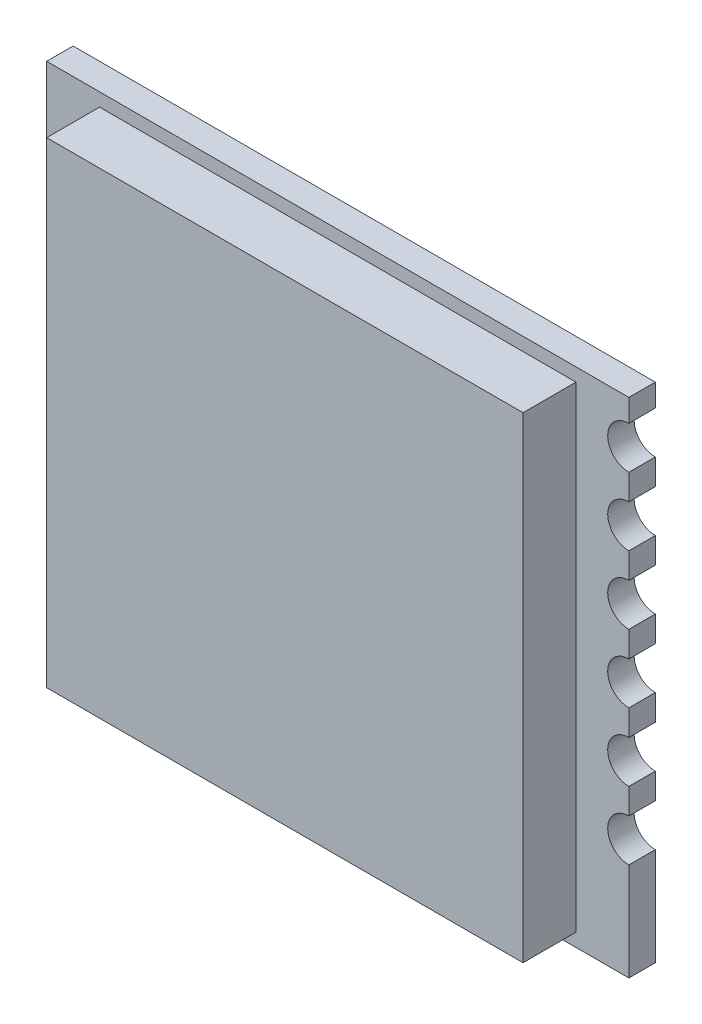
SolidWorks part; units mm, degrees
other "Детальный элемент1"
ref_plane "Спереди" through (0, 0, 0) normal (0, 0, 1) x (1, 0, 0)
ref_plane "Сверху" through (0, 0, 0) normal (0, 1, 0) x (1, 0, 0)
ref_plane "Справа" through (0, 0, 0) normal (1, 0, 0) x (0, 0, -1)
sketch "Эскиз1" plane through (0, 0, 0) normal (0, 0, 1) x (1, 0, 0)
  line L1 (11, -9.5) -> (-11, -9.5)
  line L2 (11, -9.5) -> (11, 9.5)
  line L3 (11, 9.5) -> (-11, 9.5)
  line L4 (-11, -9.5) -> (-11, 9.5)
  line L5 (11, -9.5) -> (-11, 9.5) construction
  line L6 (11, 9.5) -> (-11, -9.5) construction
  point P0 (0, 0)
extrude "Бобышка-Вытянуть1" add sketch "Эскиз1" along normal blind 1
sketch "Эскиз2" plane through (0, 0, 1) normal (0, 0, 1) x (1, 0, 0)
  line L1 (9, -9) -> (-9, -9)
  line L2 (9, -9) -> (9, 9)
  line L3 (9, 9) -> (-9, 9)
  line L4 (-9, -9) -> (-9, 9)
  line L5 (9, -9) -> (-9, 9) construction
  line L6 (9, 9) -> (-9, -9) construction
  point P0 (0, 0)
  dimension "D1" = 18
extrude "Бобышка-Вытянуть2" add sketch "Эскиз2" along normal blind 2
sketch "Эскиз3" plane through (0, 0, 3) normal (0, 0, 1) x (1, 0, 0)
  line L0 (0, 0) -> (0, 9) construction
  line L1 (9, 9) -> (-9, 9) construction
  line L2 (-11, 9.5) -> (-11, -9.5) construction
  line L3 (-11, -9.5) -> (11, -9.5) construction
  line L4 (-11, -4.2) -> (-11, -5.8)
  line L5 (-11, -1.63) -> (-11, -3.23)
  line L6 (-11, 0.94) -> (-11, -0.66)
  line L7 (-11, 3.51) -> (-11, 1.91)
  line L8 (-11, 6.08) -> (-11, 4.48)
  line L9 (11, -4.2) -> (11, -5.8)
  line L10 (11, -1.63) -> (11, -3.23)
  line L11 (11, 0.94) -> (11, -0.66)
  line L12 (11, 3.51) -> (11, 1.91)
  line L13 (11, 6.08) -> (11, 4.48)
  line L14 (11, 8.65) -> (11, 7.05)
  arc A0 (-11, -5.8) -> (-11, -4.2) centre (-11, -5) ccw
  arc A1 (-11, -3.23) -> (-11, -1.63) centre (-11, -2.43) ccw
  arc A2 (-11, -0.66) -> (-11, 0.94) centre (-11, 0.14) ccw
  arc A3 (-11, 1.91) -> (-11, 3.51) centre (-11, 2.71) ccw
  arc A4 (-11, 4.48) -> (-11, 6.08) centre (-11, 5.28) ccw
  arc A5 (11, -5.8) -> (11, -4.2) centre (11, -5) cw
  arc A6 (11, -3.23) -> (11, -1.63) centre (11, -2.43) cw
  arc A7 (11, -0.66) -> (11, 0.94) centre (11, 0.14) cw
  arc A8 (11, 1.91) -> (11, 3.51) centre (11, 2.71) cw
  arc A9 (11, 4.48) -> (11, 6.08) centre (11, 5.28) cw
  arc A10 (11, 7.05) -> (11, 8.65) centre (11, 7.85) cw
  point P5 (-11, -5)
  dimension "D2" = 5
  dimension "D1" = 4.5
  dimension "D3" = 2
extrude "Вырез-Вытянуть1" cut sketch "Эскиз3" against normal through all
sketch "Эскиз4" plane through (0, 0, 3) normal (0, 0, 1) x (1, 0, 0)
